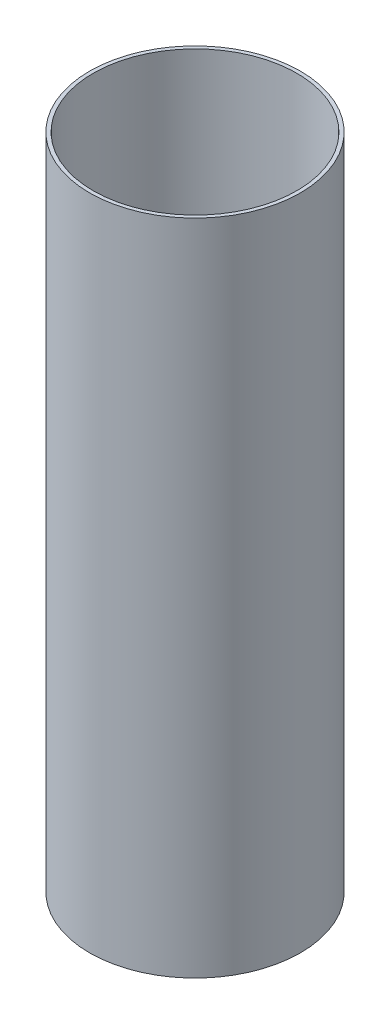
SolidWorks part; units mm, degrees
ref_plane "Front Plane" through (0, 0, 0) normal (0, 0, 1) x (1, 0, 0)
ref_plane "Top Plane" through (0, 0, 0) normal (0, 1, 0) x (1, 0, 0)
ref_plane "Right Plane" through (0, 0, 0) normal (1, 0, 0) x (0, 0, -1)
sketch "Sketch1" plane through (0, 0, 0) normal (0, 1, 0) x (1, 0, 0)
  circle A0 centre (0, 0) radius 88.9
  circle A1 centre (0, 0) radius 92.075
  dimension "D1" = 184.15
  dimension "D2" = 177.8
extrude "Boss-Extrude1" add sketch "Sketch1" along normal blind 574.675 contours A1 A0
